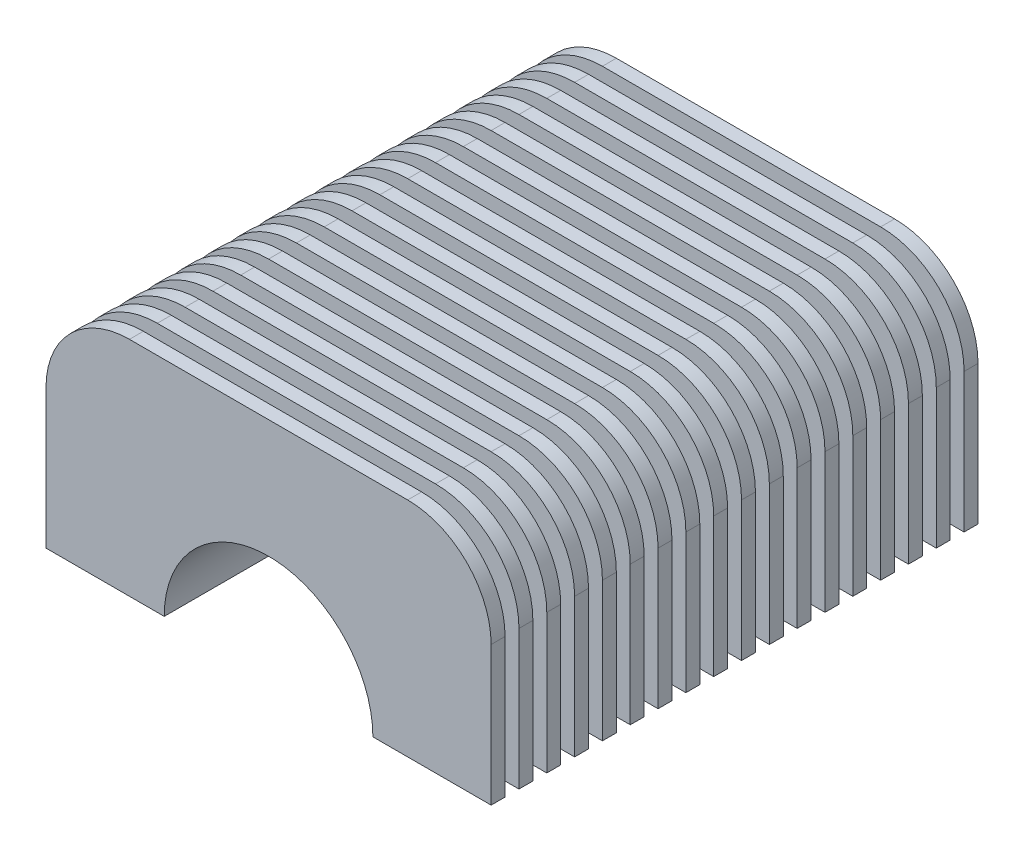
SolidWorks part; units mm, degrees
ref_plane "Płaszczyzna przednia" through (0, 0, 0) normal (0, 0, 1) x (1, 0, 0)
ref_plane "Płaszczyzna górna" through (0, 0, 0) normal (0, 1, 0) x (1, 0, 0)
ref_plane "Płaszczyzna prawa" through (0, 0, 0) normal (1, 0, 0) x (0, 0, -1)
sketch "Szkic1" plane through (0, 0, 0) normal (0, 0, 1) x (1, 0, 0)
  line L0 (22.5, 0) -> (40, 0)
  line L1 (40, 0) -> (40, 40)
  line L2 (40, 40) -> (-40, 40)
  line L3 (-40, 40) -> (-40, 0)
  line L4 (-40, 0) -> (-22.5, 0)
  arc A0 (22.5, 0) -> (-22.5, 0) centre (0, 0) ccw
  dimension "D1" = 45
  dimension "D2" = 40
  dimension "D3" = 80
extrude "Dodanie-wyciągnięcie1" add sketch "Szkic1" against normal blind 108
fillet "Zaokrąglenie1" radius 10 2 edges at (-40, 40, -54) (40, 40, -54)
sketch "Szkic2" plane through (0, 0, 0) normal (0, 0, 1) x (1, 0, 0)
  line L0 (40, 0) -> (40, 30) construction
  line L1 (30, 40) -> (-30, 40) construction
  line L2 (-40, 30) -> (-40, 0) construction
  line L3 (40, 0) -> (40, 30)
  line L4 (30, 40) -> (-30, 40)
  line L5 (-40, 30) -> (-40, 0)
  line L6 (48, 0) -> (48, 30)
  line L7 (30, 48) -> (-30, 48)
  line L8 (-48, 30) -> (-48, 0)
  line L9 (-48, 0) -> (-40, 0)
  line L10 (40, 0) -> (48, 0)
  arc A0 (40, 30) -> (30, 40) centre (30, 30) ccw construction
  arc A1 (-30, 40) -> (-40, 30) centre (-30, 30) ccw construction
  arc A2 (40, 30) -> (30, 40) centre (30, 30) ccw
  arc A3 (-30, 40) -> (-40, 30) centre (-30, 30) ccw
  arc A4 (48, 30) -> (30, 48) centre (30, 30) ccw
  arc A5 (-30, 48) -> (-48, 30) centre (-30, 30) ccw
  dimension "D1" = 8
extrude "Dodanie-wyciągnięcie2" add sketch "Szkic2" against normal blind 3
pattern_linear "Szyk liniowy1" count 18 spacing 6 along (0, 0, -1) of "Dodanie-wyciągnięcie2"
